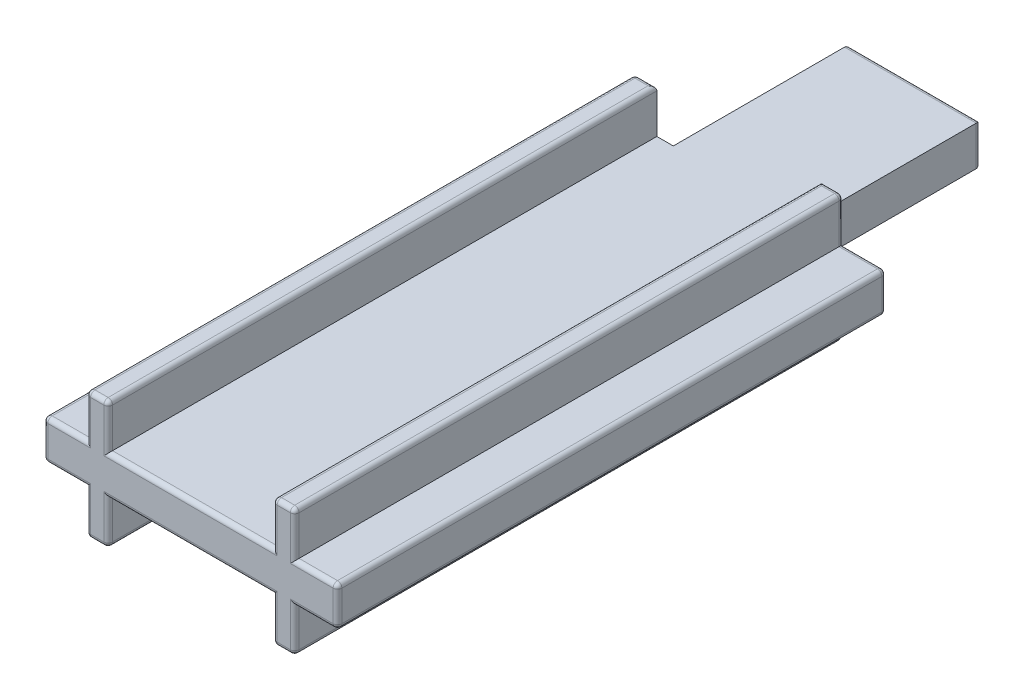
SolidWorks part; units mm, degrees
ref_plane "Ebene vorne" through (0, 0, 0) normal (0, 0, 1) x (1, 0, 0)
ref_plane "Ebene oben" through (0, 0, 0) normal (0, 1, 0) x (1, 0, 0)
ref_plane "Ebene rechts" through (0, 0, 0) normal (1, 0, 0) x (0, 0, -1)
sketch "Skizze1" plane through (0, 0, 0) normal (0, 0, 1) x (1, 0, 0)
  line L0 (-4.75, 0.9) -> (-6.7, 0.9)
  line L1 (6.7, -0.9) -> (4.75, -0.9)
  line L2 (6.7, -0.9) -> (6.7, 0.9)
  line L3 (6.7, 0.9) -> (4.75, 0.9)
  line L4 (-6.7, -0.9) -> (-6.7, 0.9)
  line L5 (6.7, -0.9) -> (-6.7, 0.9) construction
  line L6 (6.7, 0.9) -> (-6.7, -0.9) construction
  line L7 (-4.75, -2.9) -> (-3.75, -2.9)
  line L8 (-4.75, -2.9) -> (-4.75, -0.9)
  line L9 (-4.75, 2.9) -> (-3.75, 2.9)
  line L10 (-3.75, -2.9) -> (-3.75, -0.9)
  line L11 (-4.75, -2.9) -> (-3.75, 2.9) construction
  line L12 (-4.75, 2.9) -> (-3.75, -2.9) construction
  line L13 (4.75, -2.9) -> (3.75, -2.9)
  line L14 (4.75, -2.9) -> (4.75, -0.9)
  line L15 (4.75, 2.9) -> (3.75, 2.9)
  line L16 (3.75, -2.9) -> (3.75, -0.9)
  line L17 (4.75, -2.9) -> (3.75, 2.9) construction
  line L18 (4.75, 2.9) -> (3.75, -2.9) construction
  line L19 (-4.75, -0.9) -> (-6.7, -0.9)
  line L20 (-4.75, 0.9) -> (-4.75, 2.9)
  line L21 (-3.75, 0.9) -> (-3.75, 2.9)
  line L22 (3.75, -0.9) -> (-3.75, -0.9)
  line L23 (3.75, 0.9) -> (3.75, 2.9)
  line L24 (4.75, 0.9) -> (4.75, 2.9)
  line L25 (3.75, 0.9) -> (-3.75, 0.9)
  point P0 (0, 0)
  point P5 (-4.25, 0)
  point P11 (4.25, 0)
  dimension "D1" = 1.8
  dimension "D2" = 5.8
  dimension "D3" = 13.4
  dimension "D4" = 9.5
  dimension "D5" = 1
  dimension "D6" = 4.75
extrude "Aufsatz-Linear austragen1" add sketch "Skizze1" along normal blind 25
sketch "Skizze2" plane through (0, 0, 0) normal (0, 0, -1) x (-1, 0, 0)
  line L0 (-3.75, 0.9) -> (3.75, 0.9) construction
  line L1 (3, -0.9) -> (-3, -0.9)
  line L2 (3, -0.9) -> (3, 0.9)
  line L3 (3, 0.9) -> (-3, 0.9)
  line L4 (-3, -0.9) -> (-3, 0.9)
  line L5 (3, -0.9) -> (-3, 0.9) construction
  line L6 (3, 0.9) -> (-3, -0.9) construction
  point P0 (0, 0)
  dimension "D1" = 6
extrude "Aufsatz-Linear austragen2" add sketch "Skizze2" along normal blind 8
fillet "Verrundung1" radius 0.2 50 edges at (-5.725, 0.9, 25) (-4.75, 1.9, 25) (-3.75, 1.9, 25) (0, 0.9, 25) (3.75, 1.9, 25) (4.75, 1.9, 25) (5.725, 0.9, 25) (5.725, -0.9, 25) (4.75, -1.9, 25) (3.75, -1.9, 25) (0, -0.9, 25) (-3.75, -1.9, 25) (-4.75, -1.9, 25) (-5.725, -0.9, 25) (0, 0.9, -8) (-3, 0, -8) (0, -0.9, -8) (3, 0, -8) (-6.7, 0.9, 12.5) (-6.7, 0, 25) (-6.7, -0.9, 12.5) (-6.7, 0, 0) (6.7, -0.9, 12.5) (6.7, 0, 25) (6.7, 0.9, 12.5) (6.7, 0, 0) (-4.75, -2.9, 12.5) (-3.75, -2.9, 12.5) (-4.25, -2.9, 0) (3.75, -2.9, 12.5) (4.75, -2.9, 12.5) (4.25, -2.9, 0) (-3.75, 2.9, 12.5) (-4.75, 2.9, 12.5) (-4.25, 2.9, 0) (4.75, 2.9, 12.5) (3.75, 2.9, 12.5) (4.25, 2.9, 0) (4.75, 1.9, 0) (5.725, 0.9, 0) (5.725, -0.9, 0) (4.75, -1.9, 0) (-4.75, 1.9, 0) (-4.75, -1.9, 0) (-5.725, 0.9, 0) (-5.725, -0.9, 0) (-4.25, -2.9, 25) (4.25, -2.9, 25) (-4.25, 2.9, 25) (4.25, 2.9, 25)
